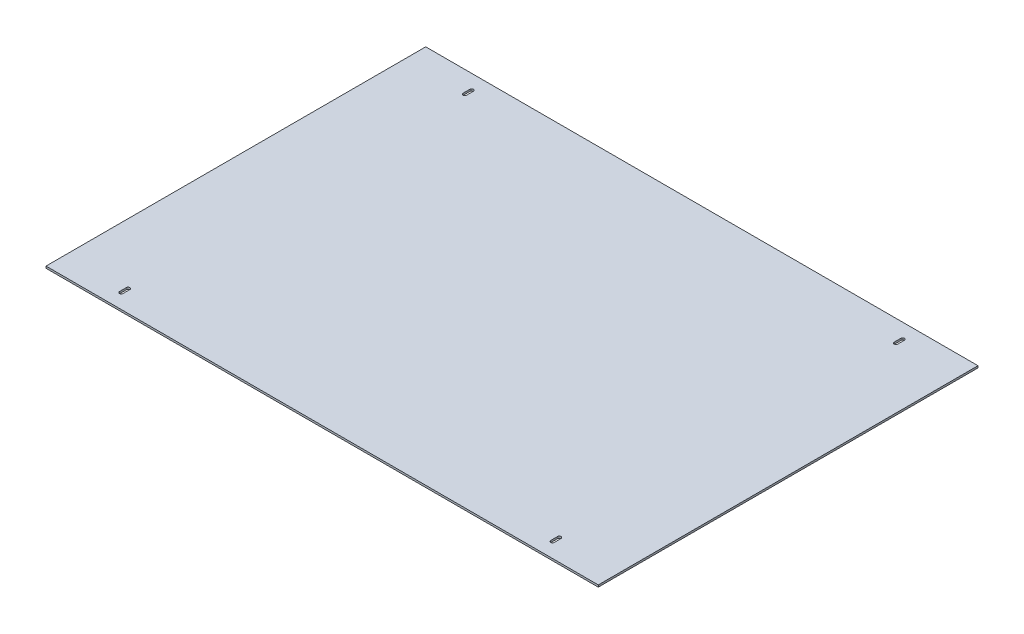
SolidWorks part; units mm, degrees
ref_plane "Front Plane" through (0, 0, 0) normal (0, 0, 1) x (1, 0, 0)
ref_plane "Top Plane" through (0, 0, 0) normal (0, 1, 0) x (1, 0, 0)
ref_plane "Right Plane" through (0, 0, 0) normal (1, 0, 0) x (0, 0, -1)
sketch "Sketch1" plane through (0, 0, 0) normal (0, 1, 0) x (1, 0, 0)
  line L1 (-357.886, -246.0625) -> (357.886, -246.0625)
  line L2 (-357.886, -246.0625) -> (-357.886, 246.0625)
  line L3 (-357.886, 246.0625) -> (357.886, 246.0625)
  line L4 (357.886, -246.0625) -> (357.886, 246.0625)
  line L5 (-357.886, -246.0625) -> (357.886, 246.0625) construction
  line L6 (-357.886, 246.0625) -> (357.886, -246.0625) construction
  point P1 (0, 0)
  dimension "D1" = 715.772
  dimension "D2" = 492.125
extrude "Boss-Extrude1" add sketch "Sketch1" along normal blind 2.54
sketch "Sketch2" plane through (0, 2.54, 0) normal (0, 1, 0) x (1, 0, 0)
  line L0 (357.886, 0) -> (-357.886, 0) construction
  line L1 (357.886, -246.0625) -> (357.886, 246.0625) construction
  line L2 (-357.886, 246.0625) -> (-357.886, -246.0625) construction
  line L3 (0, 246.0625) -> (0, -246.0625) construction
  line L4 (357.886, 246.0625) -> (-357.886, 246.0625) construction
  line L5 (-357.886, -246.0625) -> (357.886, -246.0625) construction
  line L6 (0, 246.0625) -> (0, 0) construction
  line L7 (-357.886, 122.9995) -> (357.886, 122.9995) construction
  line L8 (-357.886, 122.9995) -> (0, 122.9995) construction
  line L9 (0, 122.9995) -> (357.886, 122.9995) construction
  line L10 (338.836, 122.9995) -> (338.836, 246.0625) construction
  line L11 (338.836, 218.1225) -> (338.836, 227.0125) construction
  line L12 (336.5881, 218.1225) -> (336.5881, 227.0125)
  line L13 (341.0839, 218.1225) -> (341.0839, 227.0125)
  line L14 (338.836, 227.0125) -> (338.836, 246.0625) construction
  line L15 (-338.836, 218.1225) -> (-338.836, 227.0125) construction
  line L16 (-336.5881, 218.1225) -> (-336.5881, 227.0125)
  line L17 (-341.0839, 218.1225) -> (-341.0839, 227.0125)
  line L18 (338.836, -218.1225) -> (338.836, -227.0125) construction
  line L19 (336.5881, -218.1225) -> (336.5881, -227.0125)
  line L20 (341.0839, -218.1225) -> (341.0839, -227.0125)
  line L21 (-338.836, -218.1225) -> (-338.836, -227.0125) construction
  line L22 (-336.5881, -218.1225) -> (-336.5881, -227.0125)
  line L23 (-341.0839, -218.1225) -> (-341.0839, -227.0125)
  arc A0 (336.5881, 218.1225) -> (341.0839, 218.1225) centre (338.836, 218.1225) ccw
  arc A1 (341.0839, 227.0125) -> (336.5881, 227.0125) centre (338.836, 227.0125) ccw
  arc A2 (-336.5881, 218.1225) -> (-341.0839, 218.1225) centre (-338.836, 218.1225) cw
  arc A3 (-341.0839, 227.0125) -> (-336.5881, 227.0125) centre (-338.836, 227.0125) cw
  arc A4 (336.5881, -218.1225) -> (341.0839, -218.1225) centre (338.836, -218.1225) cw
  arc A5 (341.0839, -227.0125) -> (336.5881, -227.0125) centre (338.836, -227.0125) cw
  arc A6 (-336.5881, -218.1225) -> (-341.0839, -218.1225) centre (-338.836, -218.1225) ccw
  arc A7 (-341.0839, -227.0125) -> (-336.5881, -227.0125) centre (-338.836, -227.0125) ccw
  point P21 (338.836, 222.5675)
  point P29 (-338.836, 222.5675)
  point P36 (338.836, -222.5675)
  point P43 (-338.836, -222.5675)
  dimension "D1" = 4.4958
  dimension "D2" = 19.05
  dimension "D3" = 8.89
  dimension "D4" = 19.05
extrude "Cut-Extrude1" [suppressed] cut sketch "Sketch2" against normal blind 2.54
sketch "Sketch6" plane through (0, 2.54, 0) normal (0, 1, 0) x (1, 0, 0)
  line L0 (-279.4, 0) -> (279.4, 0) construction
  line L1 (279.4, 215.8746) -> (279.4, 246.0625) construction
  line L2 (357.886, 246.0625) -> (-357.886, 246.0625) construction
  line L3 (279.4, 218.1225) -> (279.4, 227.0125) construction
  line L4 (277.1521, 218.1225) -> (277.1521, 227.0125)
  line L5 (281.6479, 218.1225) -> (281.6479, 227.0125)
  line L6 (0, -246.0625) -> (0, 246.0625) construction
  line L7 (279.4, 222.5675) -> (279.4, -222.5675) construction
  line L8 (-279.4, 218.1225) -> (-279.4, 227.0125) construction
  line L9 (-277.1521, 218.1225) -> (-277.1521, 227.0125)
  line L10 (-281.6479, 218.1225) -> (-281.6479, 227.0125)
  line L11 (279.4, -218.1225) -> (279.4, -227.0125) construction
  line L12 (277.1521, -218.1225) -> (277.1521, -227.0125)
  line L13 (281.6479, -218.1225) -> (281.6479, -227.0125)
  line L14 (-279.4, -218.1225) -> (-279.4, -227.0125) construction
  line L15 (-277.1521, -218.1225) -> (-277.1521, -227.0125)
  line L16 (279.4, -215.8746) -> (279.4, -246.0625) construction
  line L17 (-281.6479, -218.1225) -> (-281.6479, -227.0125)
  line L18 (-279.4, -215.8746) -> (-279.4, -246.0625) construction
  line L19 (-279.4, 222.5675) -> (-279.4, -222.5675) construction
  line L20 (-279.4, 215.8746) -> (-279.4, 246.0625) construction
  arc A0 (277.1521, 218.1225) -> (281.6479, 218.1225) centre (279.4, 218.1225) ccw
  arc A1 (281.6479, 227.0125) -> (277.1521, 227.0125) centre (279.4, 227.0125) ccw
  arc A2 (277.1521, -218.1225) -> (281.6479, -218.1225) centre (279.4, -218.1225) cw
  arc A3 (281.6479, -227.0125) -> (277.1521, -227.0125) centre (279.4, -227.0125) cw
  arc A4 (-277.1521, 218.1225) -> (-281.6479, 218.1225) centre (-279.4, 218.1225) cw
  arc A5 (-281.6479, 227.0125) -> (-277.1521, 227.0125) centre (-279.4, 227.0125) cw
  arc A6 (-277.1521, -218.1225) -> (-281.6479, -218.1225) centre (-279.4, -218.1225) ccw
  arc A7 (-281.6479, -227.0125) -> (-277.1521, -227.0125) centre (-279.4, -227.0125) ccw
  point P8 (279.4, 222.5675)
  point P19 (-279.4, 222.5675)
  point P24 (279.4, -222.5675)
  point P33 (-279.4, -222.5675)
  point P36 (0, 0)
  dimension "D1" = 279.4
  dimension "D2" = 8.89
  dimension "D3" = 4.4958
  dimension "D4" = 23.495
extrude "Cut-Extrude2" cut sketch "Sketch6" against normal through all
sketch "Sketch7" [suppressed] plane through (0, 2.54, 0) normal (0, 1, 0) x (1, 0, 0)
  line L0 (-304.8, 0) -> (304.8, 0) construction
  line L1 (-304.8, 246.0625) -> (-304.8, -246.0625) construction
  line L2 (304.8, -246.0625) -> (304.8, 246.0625) construction
  line L3 (0, 246.0625) -> (0, -246.0625) construction
  line L4 (304.8, 246.0625) -> (-304.8, 246.0625) construction
  line L5 (-304.8, -246.0625) -> (304.8, -246.0625) construction
